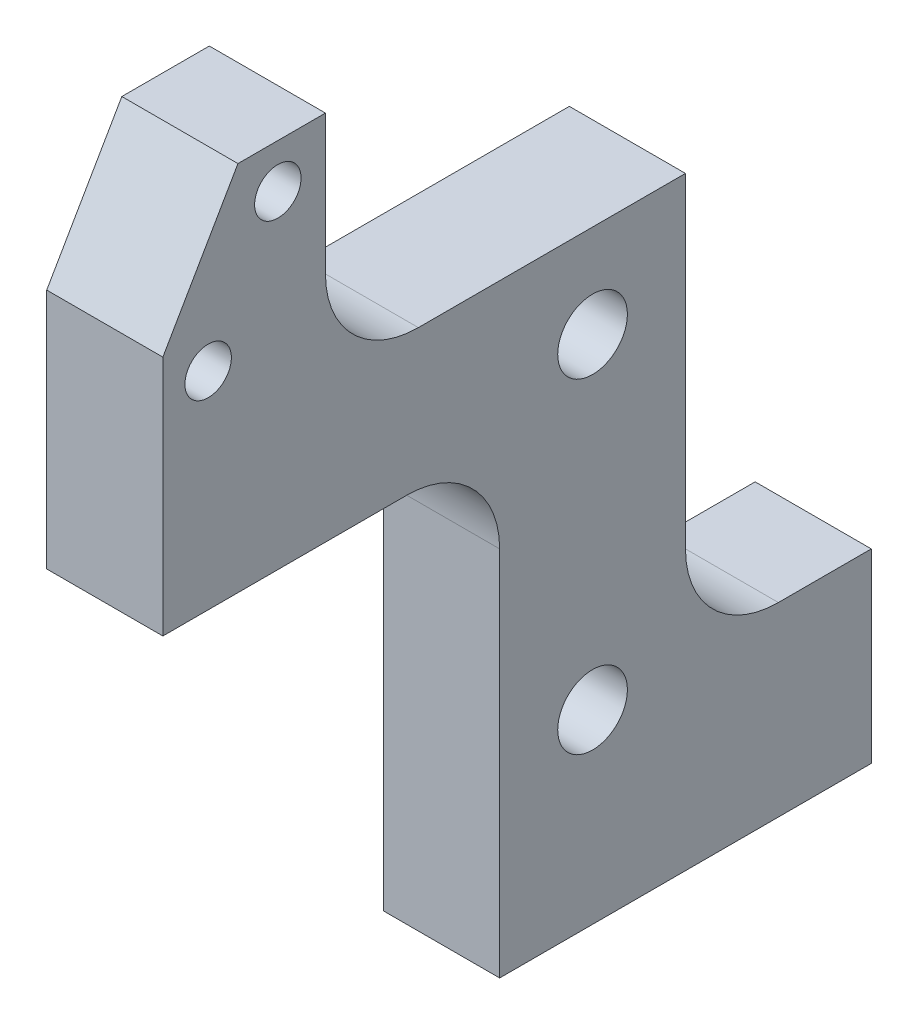
SolidWorks part; units mm, degrees
ref_plane "Front Plane" through (0, 0, 0) normal (0, 0, 1) x (1, 0, 0)
ref_plane "Top Plane" through (0, 0, 0) normal (0, 1, 0) x (1, 0, 0)
ref_plane "Right Plane" through (0, 0, 0) normal (1, 0, 0) x (0, 0, -1)
sketch "Sketch1" plane through (0, 0, 0) normal (1, 0, 0) x (0, 0, -1)
  line L0 (30.5, 0) -> (14.5, 0)
  line L1 (14.5, 0) -> (14.5, 20)
  line L2 (14.5, 20) -> (0, 20)
  line L3 (0, 20) -> (0, 30.4)
  line L4 (0, 30.4) -> (3.2332, 36)
  line L5 (3.2332, 36) -> (7, 36)
  line L6 (7, 36) -> (7, 26)
  line L7 (7, 26) -> (22.5, 26)
  line L8 (22.5, 26) -> (22.5, 8)
  line L9 (22.5, 8) -> (30.5, 8)
  line L10 (30.5, 8) -> (30.5, 0)
  line L11 (1.95, 28.91) -> (4.95, 34.1062) construction
  circle A0 centre (18.5, 8) radius 1.5
  circle A1 centre (18.5, 22) radius 1.5
  circle A2 centre (1.95, 28.91) radius 1
  circle A3 centre (4.95, 34.1062) radius 1
  dimension "D3" = 3
  dimension "D4" = 2
  dimension "D1" = 8
  dimension "D2" = 14.5
  dimension "D5" = 16
  dimension "D6" = 12
  dimension "D7" = 14
  dimension "D8" = 8
  dimension "D9" = 20
  dimension "D10" = 120
  dimension "D11" = 5.6
  dimension "D12" = 6
  dimension "D13" = 1.95
  dimension "D14" = 7.09
  dimension "D15" = 7
  dimension "D16" = 10
  dimension "D17" = 36
extrude "Boss-Extrude1" add sketch "Sketch1" along normal blind 5
fillet "Fillet1" radius 4 3 edges at (2.5, 8, -22.5) (2.5, 20, -14.5) (2.5, 26, -7)
hole_wizard "Tap Drill for M3x0.5 Tap1" positions "Sketch3" profile "Sketch2" hole size "M3x0.5" standard "ANSI Metric"
sketch "Sketch3" plane through (0, 0, 0) normal (0, -1, 0) x (-1, 0, 0)
  line L0 (-5, 14.5) -> (-5, 30.5) construction
  line L1 (-5, 30.5) -> (0, 30.5) construction
  point P0 (-2.5, 17.5)
  point P2 (-2.5, 27.5)
  dimension "D1" = 2.5
  dimension "D2" = 3
  dimension "D3" = 10
sketch "Sketch2" plane through (2.5, 0, -17.5) normal (1, 0, 0) x (0, 0, -1)
  line L0 (0, 0) -> (0, 4)
  line L1 (0, 4) -> (1.25, 4)
  line L2 (1.25, 4) -> (1.25, 0)
  line L5 (1.25, 0) -> (0, 0)
  line L10 (0, 4) -> (-1.25, 4) construction
  line L11 (0, -6.35) -> (0, 107.95) construction
  dimension "Hole Dia." = 2.5
  dimension "Hole Depth" = 4
  dimension "Drill Angle" = 180
chamfer "Chamfer1" distance 1.5 angle 45 2 edges at (0, 8, -20) (0, 22, -20)
